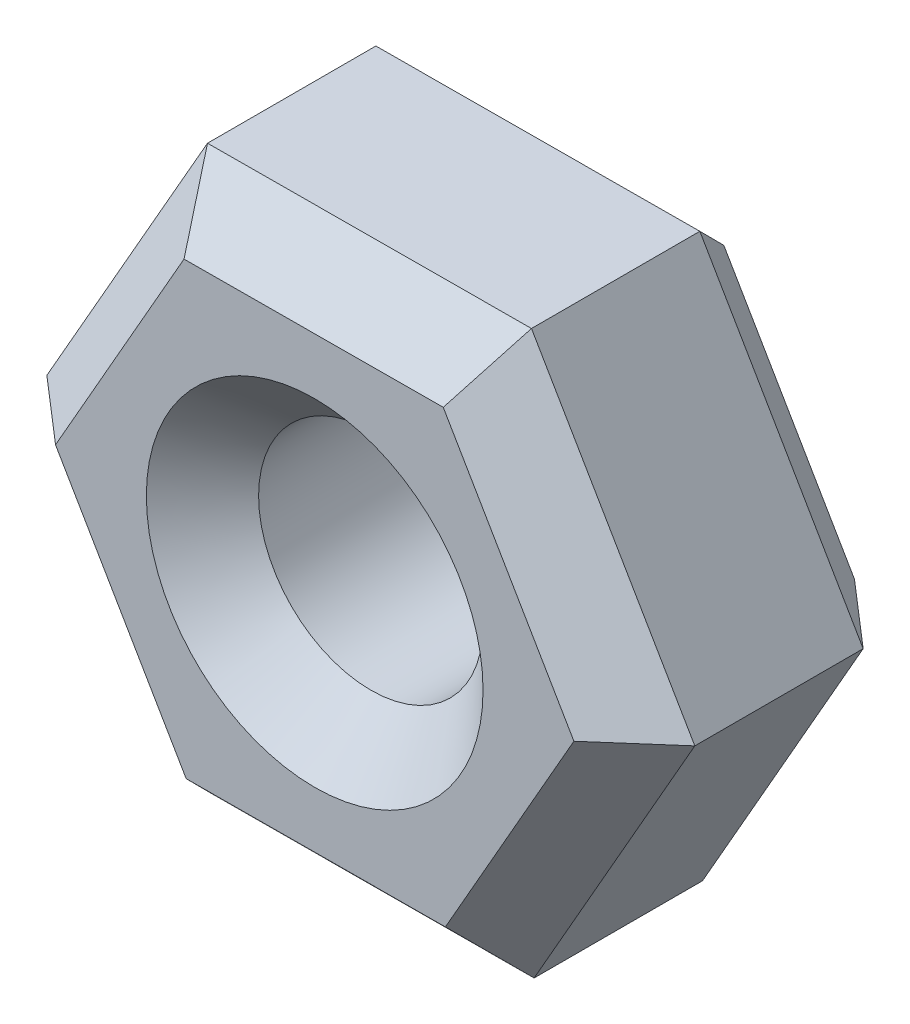
SolidWorks part; units mm, degrees
ref_plane "Front Plane" through (0, 0, 0) normal (0, 0, 1) x (1, 0, 0)
ref_plane "Top Plane" through (0, 0, 0) normal (0, 1, 0) x (1, 0, 0)
ref_plane "Right Plane" through (0, 0, 0) normal (1, 0, 0) x (0, 0, -1)
sketch "Sketch2" plane through (0, 0, 0) normal (0, 0, 1) x (1, 0, 0)
  line L1 (-33.2046, 16.9637) -> (-38.978, 16.9363)
  line L2 (-38.978, 16.9363) -> (-41.841, 11.9227)
  line L3 (-41.841, 11.9227) -> (-38.9305, 6.9364)
  line L4 (-38.9305, 6.9364) -> (-33.1571, 6.9639)
  line L5 (-33.1571, 6.9639) -> (-30.2941, 11.9775)
  line L6 (-30.2941, 11.9775) -> (-33.2046, 16.9637)
  circle A0 centre (-36.0675, 11.9501) radius 2
  circle A1 centre (-36.0675, 11.9501) radius 5 construction
  point P2 (-31.7256, 9.4707)
  dimension "D1" = 10
  dimension "D2" = 4
extrude "Boss-Extrude1" add sketch "Sketch2" along normal blind 5
chamfer "Chamfer2" distance 1 angle 45 14 edges at (-34.0675, 11.9501, 5) (-31.7256, 9.4707, 5) (-36.0438, 6.9501, 5) (-40.3858, 9.4296, 5) (-40.4095, 14.4295, 5) (-36.0913, 16.95, 5) (-31.7493, 14.4706, 5) (-34.0675, 11.9501, 0) (-36.0913, 16.95, 0) (-40.4095, 14.4295, 0) (-40.3858, 9.4296, 0) (-36.0438, 6.9501, 0) (-31.7256, 9.4707, 0) (-31.7493, 14.4706, 0)
